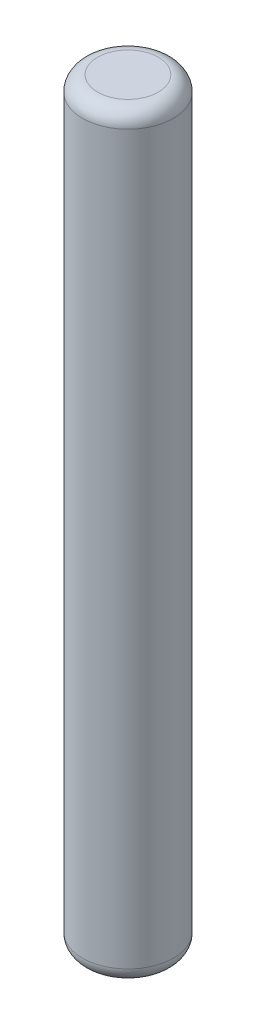
SolidWorks part; units mm, degrees
ref_plane "Front" through (0, 0, 0) normal (0, 0, 1) x (1, 0, 0)
ref_plane "Top" through (0, 0, 0) normal (0, 1, 0) x (1, 0, 0)
ref_plane "Right" through (0, 0, 0) normal (1, 0, 0) x (0, 0, -1)
sketch "Sketch1" plane through (0, 0, 0) normal (0, 1, 0) x (1, 0, 0)
  circle A0 centre (0, 0) radius 1.5
  dimension "D1" = 3
extrude "Boss-Extrude1" add sketch "Sketch1" along normal blind 25
fillet "Fillet1" radius 0.5 2 edges at (0, 0, 1.5) (0, 25, 1.5)
